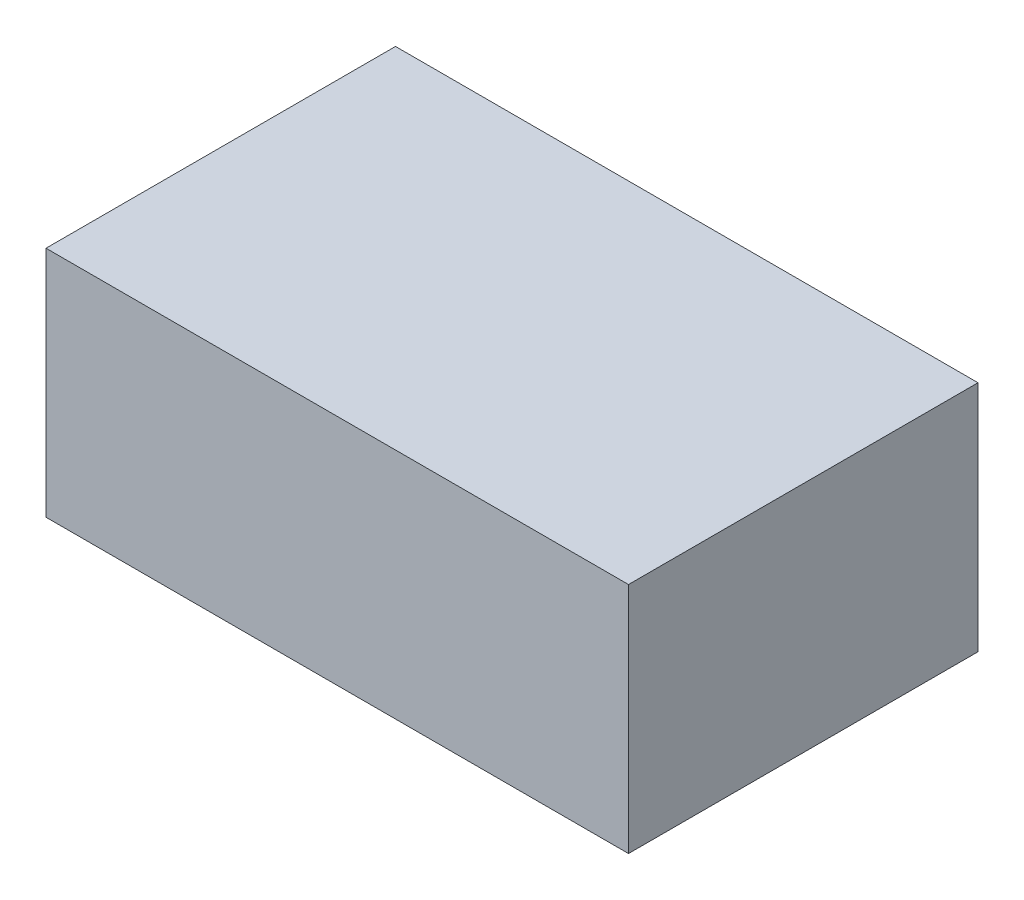
SolidWorks part; units mm, degrees
material "ASTM A36 Steel"
ref_plane "Front Plane" through (0, 0, 0) normal (0, 0, 1) x (1, 0, 0)
ref_plane "Top Plane" through (0, 0, 0) normal (0, 1, 0) x (1, 0, 0)
ref_plane "Right Plane" through (0, 0, 0) normal (1, 0, 0) x (0, 0, -1)
sketch "Sketch1" plane through (0, 0, 0) normal (0, 0, 1) x (1, 0, 0)
  line L1 (15.875, 6.35) -> (-15.875, 6.35)
  line L2 (15.875, 6.35) -> (15.875, -6.35)
  line L3 (15.875, -6.35) -> (-15.875, -6.35)
  line L4 (-15.875, 6.35) -> (-15.875, -6.35)
  line L5 (15.875, 6.35) -> (-15.875, -6.35) construction
  line L6 (15.875, -6.35) -> (-15.875, 6.35) construction
  point P0 (0, 0)
  dimension "D1" = 12.7
  dimension "D2" = 31.75
extrude "Boss-Extrude1" add sketch "Sketch1" along normal blind 19.05
